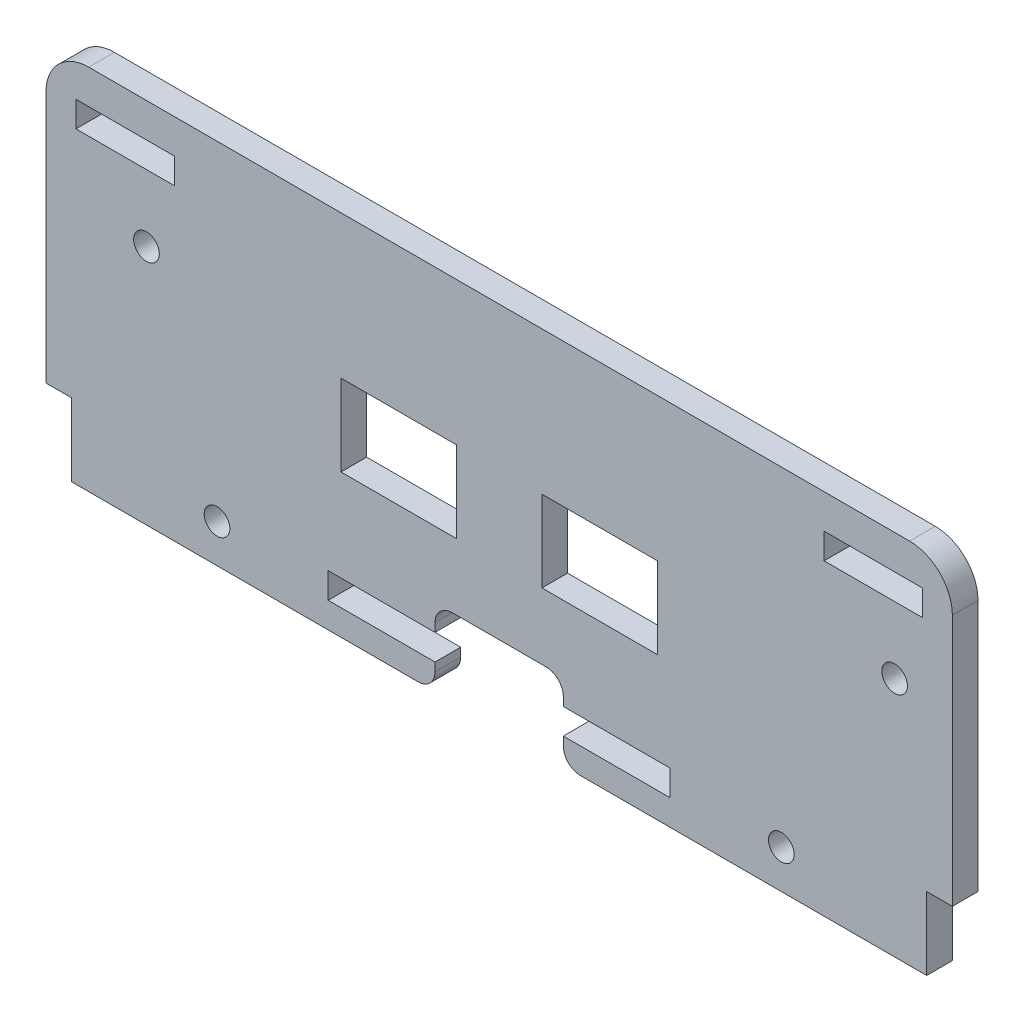
SolidWorks part; units mm, degrees
other "Marcação1"
sketch "Esboço7" plane through (-68, 31.5, 3) normal (-0.6758, 0.2828, 0.6807) x (0.7271, 0.1043, 0.6785)
sketch "Esboço8" plane through (-68, 31.5, 3) normal (-0.6758, 0.2828, 0.6807) x (0.7271, 0.1043, 0.6785)
sketch "Esboço9" plane through (-60.5, 31.5, 3) normal (-0.6758, 0.2828, 0.6807) x (0.7271, 0.1043, 0.6785)
sketch "Esboço12" plane through (-60.5, 31.5, 3) normal (-0.6758, 0.2828, 0.6807) x (0.7271, 0.1043, 0.6785)
sketch "Esboço14" plane through (-60.5, 31.5, 3) normal (-0.6758, 0.2828, 0.6807) x (0.7271, 0.1043, 0.6785)
sketch "Esboço15" plane through (-60.5, 36.25, 3) normal (-0.6758, 0.2828, 0.6807) x (0.7271, 0.1043, 0.6785)
sketch "Esboço18" plane through (-60.5, 33.25, 3) normal (-0.6758, 0.2828, 0.6807) x (0.7271, 0.1043, 0.6785)
sketch "Esboço20" plane through (-60.5, 29.8, 3) normal (-0.6758, 0.2828, 0.6807) x (0.7271, 0.1043, 0.6785)
sketch "Esboço22" plane through (-60.5, 29.8, 3) normal (-0.6758, 0.2828, 0.6807) x (0.7271, 0.1043, 0.6785)
material "Acrylic (Medium-high impact)"
ref_plane "Plano frontal" through (0, 0, 0) normal (0, 0, 1) x (1, 0, 0)
ref_plane "Plano superior" through (0, 0, 0) normal (0, 1, 0) x (1, 0, 0)
ref_plane "Plano direito" through (0, 0, 0) normal (1, 0, 0) x (0, 0, -1)
sketch "Esboço1" plane through (0, 0, 0) normal (0, 0, 1) x (1, 0, 0)
  line L1 (-50, -21.5) -> (50, -21.5)
  line L2 (-50, -21.5) -> (-50, 21.5)
  line L3 (-50, 21.5) -> (50, 21.5)
  line L4 (50, -21.5) -> (50, 21.5)
  line L5 (-50, -21.5) -> (50, 21.5) construction
  line L6 (-50, 21.5) -> (50, -21.5) construction
  point P0 (0, 0)
  dimension "D1" = 100
  dimension "D2" = 43
extrude "Ressalto-extrusão1" add sketch "Esboço1" along normal mid plane 3
sketch "Esboço2" plane through (0, 0, 1.5) normal (0, 0, 1) x (1, 0, 0)
  line L21 (-20, -15.5) -> (-7.5, -15.5)
  line L22 (-20, -15.5) -> (-20, -18.5)
  line L23 (-20, -18.5) -> (-7.5, -18.5)
  line L24 (20, -15.5) -> (20, -18.5)
  line L25 (-20, -15.5) -> (20, -18.5) construction
  line L26 (-20, -18.5) -> (20, -15.5) construction
  line L27 (0, -1.65) -> (0, 1.65) construction
  line L30 (-7.5, -18.5) -> (-7.5, -21.5)
  line L31 (-7.5, -21.5) -> (7.5, -21.5)
  line L32 (7.5, -18.5) -> (7.5, -21.5)
  line L33 (-50, -21.5) -> (50, -21.5) construction
  line L34 (7.5, -18.5) -> (20, -18.5)
  line L37 (-7.5, -15.5) -> (-7.5, -12.5)
  line L38 (-7.5, -12.5) -> (7.5, -12.5)
  line L39 (7.5, -15.5) -> (7.5, -12.5)
  line L40 (7.5, -15.5) -> (20, -15.5)
  circle A2 centre (-33, -17) radius 1.5
  circle A4 centre (33, -17) radius 1.5
  point P13 (0, -21.5)
  point P14 (0, -17)
  dimension "D4" = 13
  dimension "D8" = 3
  dimension "D2" = 3
  dimension "D3" = 15
  dimension "D5" = 3
  dimension "D6" = 3
  dimension "D13" = 40
extrude "Corte-extrusão1" cut sketch "Esboço2" against normal through all
sketch "Sketch7" plane through (0, 0, 0) normal (0, 0, 1) x (1, 0, 0)
  line L0 (0, -1.65) -> (0, 1.65) construction
  line L1 (-18.5, 4.75) -> (-5, 4.75)
  line L2 (-18.5, 4.75) -> (-18.5, -4.75)
  line L3 (-18.5, -4.75) -> (-5, -4.75)
  line L4 (-5, 4.75) -> (-5, -4.75)
  line L9 (5, 4.75) -> (5, -4.75)
  line L10 (18.5, -4.75) -> (5, -4.75)
  line L11 (18.5, 4.75) -> (18.5, -4.75)
  line L12 (18.5, 4.75) -> (5, 4.75)
  point P5 (-18.5, 0)
  dimension "D1" = 13.5
  dimension "D2" = 9.5
  dimension "D3" = 10
extrude "Cut-Extrude6" cut sketch "Sketch7" against normal through all both and the other way through all
sketch "Sketch8" plane through (0, 0, 0) normal (0, 0, 1) x (1, 0, 0)
  line L9 (0, -1.65) -> (0, 1.65) construction
  line L10 (-50, 21.5) -> (-53, 21.5)
  line L11 (-50, 21.5) -> (-50, -13)
  line L12 (-50, -13) -> (-53, -13)
  line L13 (-53, 21.5) -> (-53, -13)
  line L14 (53, 21.5) -> (53, -13)
  line L15 (50, -13) -> (53, -13)
  line L16 (50, 21.5) -> (50, -13)
  line L17 (50, 21.5) -> (53, 21.5)
  line L18 (-50, -21.5) -> (-7.5, -21.5) construction
  dimension "D1" = 8.5
  dimension "D2" = 3
extrude "Boss-Extrude1" add sketch "Sketch8" along normal mid plane 3
fillet "Fillet3" radius 2 4 edges at (7.5, -12.5, 0) (-7.5, -12.5, 0) (7.5, -21.5, 0) (-7.5, -21.5, 0)
fillet "Fillet4" radius 5 2 edges at (53, 21.5, 0) (-53, 21.5, 0)
sketch "Sketch6" plane through (0, 0, 0) normal (0, 0, 1) x (1, 0, 0)
  line L0 (-53, 16.5) -> (-53, -13) construction
  line L15 (48, 21.5) -> (-48, 21.5) construction
  line L23 (0, -1.65) -> (0, 1.65) construction
  line B0 (-40.5, 14.0307) -> (-40.5043, 14.0307)
  line B1 (-37, 6.0307) -> (-37, 0.0307)
  line B2 (-39, -1.9693) -> (-40.5043, -1.9693)
  line B3 (-50, 12.0307) -> (-50, 0.0307)
  line B4 (-37, 6.0307) -> (-50, 6.0307) construction
  line B5 (-46.64, 15.7807) -> (-45.07, 18.5)
  line B6 (-45.07, 18.5) -> (-41.93, 18.5)
  line B7 (-41.93, 18.5) -> (-40.36, 15.7807)
  line B8 (-40.36, 15.7807) -> (-40.9374, 14.7807)
  line B9 (-46.0626, 14.7807) -> (-46.64, 15.7807)
  line B10 (-46.4957, 14.0307) -> (-48, 14.0307)
  line B11 (-46.0626, -2.7193) -> (-46.64, -3.7193)
  line B12 (-40.36, -3.7193) -> (-40.9374, -2.7193)
  line B13 (-41.93, -6.4386) -> (-40.36, -3.7193)
  line B14 (-45.07, -6.4386) -> (-41.93, -6.4386)
  line B15 (-46.64, -3.7193) -> (-45.07, -6.4386)
  line B16 (-46.4957, -1.9693) -> (-48, -1.9693)
  arc B17 (-45.855, 14.421) -> (-41.145, 14.421) centre (-43.5, 15.7807) cw construction
  arc B18 (-45.855, -2.3597) -> (-41.145, -2.3597) centre (-43.5, -3.7193) ccw construction
  arc B19 (-46.0626, -2.7193) -> (-46.4957, -1.9693) centre (-46.4957, -2.4693) ccw
  arc B20 (-40.9374, -2.7193) -> (-40.5043, -1.9693) centre (-40.5043, -2.4693) cw
  arc B21 (-46.4957, 14.0307) -> (-46.0626, 14.7807) centre (-46.4957, 14.5307) ccw
  arc B22 (-40.5043, 14.0307) -> (-40.9374, 14.7807) centre (-40.5043, 14.5307) cw
  arc B23 (-48, 14.0307) -> (-50, 12.0307) centre (-48, 12.0307) ccw
  arc B24 (-48, -1.9693) -> (-50, 0.0307) centre (-48, 0.0307) cw
  arc B25 (-37, 0.0307) -> (-39, -1.9693) centre (-39, 0.0307) cw
  arc B26 (-39, 14.0307) -> (-37, 12.0307) centre (-39, 12.0307) cw
  line B27 (-37, 12.0307) -> (-37, 6.0307)
  line B28 (-39, 14.0307) -> (-40.5, 14.0307)
  line B29 (40.5, 14.0307) -> (40.5043, 14.0307)
  line B30 (37, 6.0307) -> (37, 0.0307)
  line B31 (39, -1.9693) -> (40.5043, -1.9693)
  line B32 (50, 12.0307) -> (50, 0.0307)
  line B33 (46.64, 15.7807) -> (45.07, 18.5)
  line B34 (45.07, 18.5) -> (41.93, 18.5)
  line B35 (41.93, 18.5) -> (40.36, 15.7807)
  line B36 (40.36, 15.7807) -> (40.9374, 14.7807)
  line B37 (46.0626, 14.7807) -> (46.64, 15.7807)
  line B38 (46.4957, 14.0307) -> (48, 14.0307)
  line B39 (46.0626, -2.7193) -> (46.64, -3.7193)
  line B40 (40.36, -3.7193) -> (40.9374, -2.7193)
  line B41 (41.93, -6.4386) -> (40.36, -3.7193)
  line B42 (45.07, -6.4386) -> (41.93, -6.4386)
  line B43 (46.64, -3.7193) -> (45.07, -6.4386)
  line B44 (46.4957, -1.9693) -> (48, -1.9693)
  arc B45 (45.855, 14.421) -> (41.145, 14.421) centre (43.5, 15.7807) ccw construction
  arc B46 (45.855, -2.3597) -> (41.145, -2.3597) centre (43.5, -3.7193) cw construction
  arc B47 (46.0626, -2.7193) -> (46.4957, -1.9693) centre (46.4957, -2.4693) cw
  arc B48 (40.9374, -2.7193) -> (40.5043, -1.9693) centre (40.5043, -2.4693) ccw
  arc B49 (46.4957, 14.0307) -> (46.0626, 14.7807) centre (46.4957, 14.5307) cw
  arc B50 (40.5043, 14.0307) -> (40.9374, 14.7807) centre (40.5043, 14.5307) ccw
  arc B51 (48, 14.0307) -> (50, 12.0307) centre (48, 12.0307) cw
  arc B52 (48, -1.9693) -> (50, 0.0307) centre (48, 0.0307) ccw
  arc B53 (37, 0.0307) -> (39, -1.9693) centre (39, 0.0307) ccw
  arc B54 (39, 14.0307) -> (37, 12.0307) centre (39, 12.0307) ccw
  line B55 (37, 12.0307) -> (37, 6.0307)
  line B56 (39, 14.0307) -> (40.5, 14.0307)
  dimension "D1" = 3
  dimension "D2" = 3
sketch_block_instance "Corte Gy Completo-3"
sketch_block "Corte Gy Completo" parameters "D3"=0.5, "D4"=2, "D5"=0.5, "D1"=3.14, "D2"=19.5
sketch_block_instance "Corte Gy Completo-4"
extrude "Corte Gy-VL53L0" [suppressed] cut sketch "Sketch6" against normal through all both and the other way through all
sketch "Sketch9" plane through (0, 0, 0) normal (0, 0, 1) x (1, 0, 0)
  line L0 (-53, 16.5) -> (-53, -13) construction
  line L1 (-49.5, 17.5) -> (-38, 17.5)
  line L2 (-49.5, 17.5) -> (-49.5, 14.5)
  line L3 (-49.5, 14.5) -> (-38, 14.5)
  line L4 (-38, 17.5) -> (-38, 14.5)
  line L5 (48, 21.5) -> (-48, 21.5) construction
  line L8 (0, -1.65) -> (0, 1.65) construction
  line L9 (38, 17.5) -> (38, 14.5)
  line L10 (49.5, 14.5) -> (38, 14.5)
  line L11 (49.5, 17.5) -> (49.5, 14.5)
  line L12 (49.5, 17.5) -> (38, 17.5)
  circle A0 centre (-41.25, 6.7) radius 1.5
  circle A1 centre (46.25, 6.7) radius 1.5
  arc A4 (-48, 21.5) -> (-53, 16.5) centre (-48, 16.5) ccw construction
  point P6 (-50, 16.787)
  point P7 (-43.75, 14.5)
  point P11 (-50.4836, 18.5)
  point P20 (43.75, 14.5)
  dimension "D1" = 3
  dimension "D4" = 2.5
  dimension "D7" = 4
  dimension "D8" = 2.5
  dimension "D3" = 7.8
  dimension "D9" = 7.8
  dimension "D2" = 3
  dimension "D5" = 11.5
  dimension "D6" = 3.5
  dimension "D10" = 3.1972
extrude "Corte Gy-53LDK" cut sketch "Sketch9" against normal through all both and the other way through all
